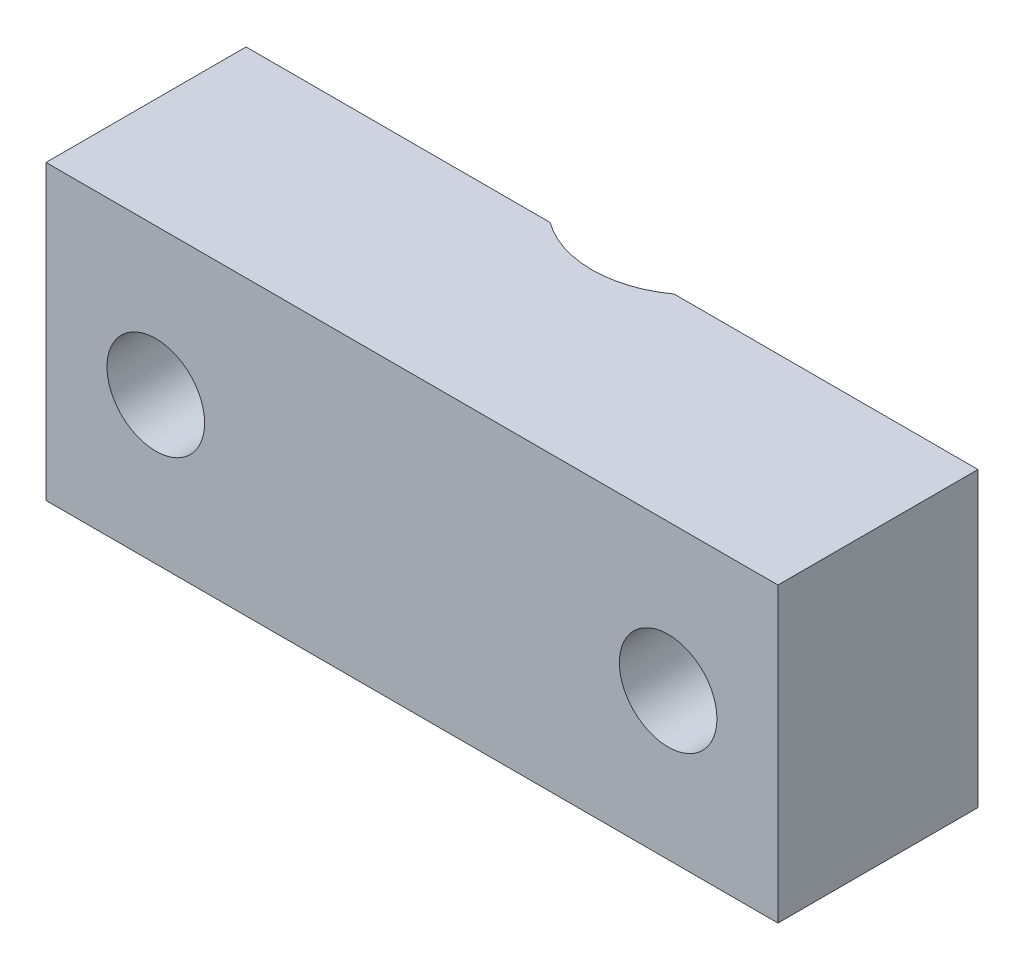
SolidWorks part; units mm, degrees
ref_plane "Front Plane" through (0, 0, 0) normal (0, 0, 1) x (1, 0, 0)
ref_plane "Top Plane" through (0, 0, 0) normal (0, 1, 0) x (1, 0, 0)
ref_plane "Right Plane" through (0, 0, 0) normal (1, 0, 0) x (0, 0, -1)
sketch "Sketch1" plane through (0, 0, 0) normal (0, 0, 1) x (1, 0, 0)
  line L1 (3.3177, 25.5562) -> (-26.6823, 25.5562)
  line L2 (3.3177, 25.5562) -> (3.3177, 37.5562)
  line L3 (3.3177, 37.5562) -> (-26.6823, 37.5562)
  line L4 (-26.6823, 25.5562) -> (-26.6823, 37.5562)
  circle A0 centre (-22.1823, 31.5562) radius 2
  circle A1 centre (-1.1823, 31.5562) radius 2
  dimension "D1" = 4
extrude "Boss-Extrude1" add sketch "Sketch1" along normal blind 8.2
sketch "Sketch2" plane through (0, 25.5562, 0) normal (0, -1, 0) x (-1, 0, 0)
  line L0 (26.6823, -8.2) -> (-3.3177, -8.2) construction
  line L1 (-3.3177, -8.2) -> (-3.3177, 0) construction
  circle A0 centre (11.6823, 3.5) radius 6.5
  dimension "D3" = 13
  dimension "D1" = 11.7
  dimension "D2" = 15
extrude "Cut-Extrude1" cut sketch "Sketch2" against normal blind 7.2
sketch "Sketch3" plane through (0, 25.5562, 0) normal (0, -1, 0) x (-1, 0, 0)
  circle A0 centre (11.6823, 3.5) radius 5.35
  arc A3 (6.2051, 0) -> (17.1595, 0) centre (11.6823, 3.5) ccw construction
  dimension "D1" = 10.7
extrude "Cut-Extrude2" cut sketch "Sketch3" against normal blind 9.9
sketch "Sketch4" plane through (0, 25.5562, 0) normal (0, -1, 0) x (-1, 0, 0)
  circle A0 centre (11.6823, 3.5) radius 4.325
  arc A1 (6.2051, 0) -> (17.1595, 0) centre (11.6823, 3.5) ccw construction
  dimension "D1" = 8.65
extrude "Cut-Extrude3" cut sketch "Sketch4" against normal blind 13.9
sketch "Sketch5" plane through (0, 25.5562, 0) normal (0, -1, 0) x (-1, 0, 0)
  line L0 (9.2701, -4.1286) -> (5.3363, 1.1915)
  line L1 (5.3363, 1.1915) -> (18.0087, 1.1915)
  line L2 (18.0087, 1.1915) -> (14.0988, -4.1228)
  arc A0 (9.2701, -4.1286) -> (14.0988, -4.1228) centre (11.6823, -2.345) ccw
  dimension "D1" = 6
extrude "Cut-Extrude4" cut sketch "Sketch5" along normal blind 1.4 from offset 5.7
